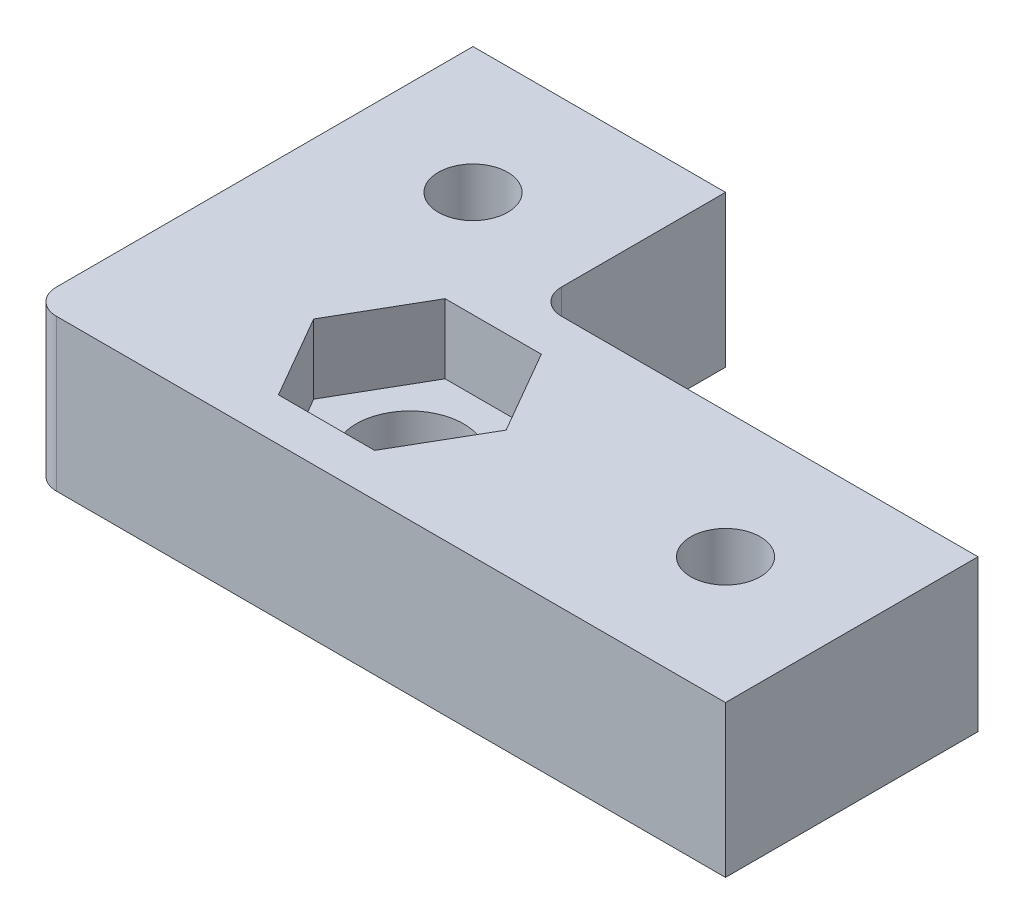
SolidWorks part; units mm, degrees
ref_plane "Alzado" through (0, 0, 0) normal (0, 0, 1) x (1, 0, 0)
ref_plane "Planta" through (0, 0, 0) normal (0, 1, 0) x (1, 0, 0)
ref_plane "Vista lateral" through (0, 0, 0) normal (1, 0, 0) x (0, 0, -1)
sketch "Croquis1" plane through (0, 0, 0) normal (0, 1, 0) x (1, 0, 0)
  line L0 (25, 65) -> (25, 25)
  line L1 (0, 0) -> (65, 0)
  line L2 (0, 0) -> (0, 65)
  line L3 (0, 65) -> (25, 65)
  line L4 (65, 0) -> (65, 25)
  line L5 (25, 25) -> (65, 25)
  line L6 (-55, 0) -> (55, 0) construction
  line L7 (0, -55) -> (0, 55) construction
  dimension "D1" = 25
  dimension "D2" = 25
  dimension "D3" = 65
  dimension "D4" = 65
extrude "Saliente-Extruir1" add sketch "Croquis1" along normal blind 12
sketch "Croquis2" plane through (0, 12, 0) normal (0, 1, 0) x (1, 0, 0)
  line L0 (0, 65) -> (0, 0)
  line L1 (0, -6.6) -> (0, 6.6) construction
  line L2 (25, 65) -> (0, 65) construction
  line L3 (0, 0) -> (65, 0)
  line L4 (-6.6, 0) -> (6.6, 0) construction
  line L5 (65, 0) -> (65, 25) construction
  line L6 (65, 0) -> (65, 5)
  line L7 (65, 5) -> (37.4, 5)
  line L8 (5, 5) -> (5, 12.6)
  line L9 (5, 65) -> (0, 65)
  line L10 (12.6, 5) -> (5, 5)
  line L11 (32.6, 5) -> (17.4, 5)
  line L12 (12.6, 5) -> (12.6, 6)
  line L13 (12.6, 6) -> (17.4, 6)
  line L14 (17.4, 5) -> (17.4, 6)
  line L15 (5, 17.4) -> (5, 65)
  line L16 (32.6, 5) -> (32.6, 6)
  line L17 (32.6, 6) -> (37.4, 6)
  line L18 (37.4, 5) -> (37.4, 6)
  line L19 (5, 17.4) -> (6, 17.4)
  line L21 (5, 12.6) -> (6, 12.6)
  line L22 (6, 17.4) -> (6, 12.6)
  dimension "D1" = 5
  dimension "D2" = 5
  dimension "D3" = 1
  dimension "D4" = 7.6
  dimension "D5" = 4.8
  dimension "D6" = 15.2
extrude "Saliente-Extruir2" add sketch "Croquis2" along normal blind 38
sketch "Croquis8" plane through (0, 50, 0) normal (0, 1, 0) x (1, 0, 0)
  line L0 (5, 17.4) -> (5, 65) construction
  line L1 (5, 25) -> (45, 25)
  line L2 (5, 25) -> (5, 5)
  line L3 (5, 5) -> (45, 5)
  line L4 (45, 25) -> (45, 5)
  line L5 (65, 5) -> (37.4, 5) construction
  dimension "D1" = 20
  dimension "D2" = 40
extrude "Cortar-Extruir5" cut sketch "Croquis8" against normal blind 20
sketch "Croquis3" plane through (0, 12, 0) normal (0, 1, 0) x (1, 0, 0)
  line L1 (5, 5) -> (5, 65) construction
  line L2 (65, 5) -> (5, 5) construction
  circle A0 centre (25, 15) radius 4.25
  dimension "D3" = 8.5
  dimension "D1" = 20
  dimension "D2" = 10
extrude "Cortar-Extruir1" cut sketch "Croquis3" against normal through all
sketch "Croquis4" plane through (0, 12, 0) normal (0, 1, 0) x (1, 0, 0)
  line L1 (32.621, 15) -> (28.8105, 21.6)
  line L2 (28.8105, 21.6) -> (21.1895, 21.6)
  line L3 (21.1895, 21.6) -> (17.379, 15)
  line L4 (17.379, 15) -> (21.1895, 8.4)
  line L5 (21.1895, 8.4) -> (28.8105, 8.4)
  line L6 (28.8105, 8.4) -> (32.621, 15)
  circle A0 centre (25, 15) radius 6.6 construction
  dimension "D1" = 13.2
extrude "Cortar-Extruir2" cut sketch "Croquis4" against normal blind 5.5
fillet "Redondeo1" radius 2 1 edges at (25, 6, -25)
sketch "Croquis5" plane through (0, 12, 0) normal (0, 1, 0) x (1, 0, 0)
  line L0 (25, 65) -> (5, 65) construction
  line L1 (12.6, 65) -> (17.4, 65)
  line L2 (12.6, 65) -> (12.6, 30)
  line L3 (12.6, 30) -> (17.4, 30)
  line L4 (17.4, 65) -> (17.4, 30)
  line L5 (5, 5) -> (5, 65) construction
  line L6 (65, 5) -> (65, 25) construction
  line L7 (65, 17.4) -> (50, 17.4)
  line L8 (65, 17.4) -> (65, 12.6)
  line L9 (65, 12.6) -> (50, 12.6)
  line L10 (50, 17.4) -> (50, 12.6)
  line L11 (65, 5) -> (37.4, 5) construction
  dimension "D1" = 35
  dimension "D2" = 4.8
  dimension "D3" = 7.6
  dimension "D4" = 15
  dimension "D5" = 7.6
extrude "Saliente-Extruir3" add sketch "Croquis5" along normal blind 1
draft "Ángulo de salida1" type of draft neutral plane draft angle 15 faces to draft 6 face at (57.5, 12.5, -17.4) face at (50, 12.5, -15) face at (57.5, 12.5, -12.6) face at (12.6, 12.5, -47.5) face at (15, 12.5, -30) face at (17.4, 12.5, -47.5) neutral plane through (0, 12, 0) neutral plane normal (0, 1, 0) parameters "D1"=15
draft "Ángulo de salida2" type of draft neutral plane draft angle 15 faces to draft 6 face at (15, 30, -5.5) face at (35, 30, -5.5) face at (37.4, 21, -5.5) face at (32.6, 21, -5.5) face at (17.4, 21, -5.5) face at (12.6, 21, -5.5) neutral plane through (65, 50, -5) neutral plane normal (0, 0, -1) parameters "D1"=15
fillet "Redondeo2" radius 2 1 edges at (0, 25, 0)
draft "Ángulo de salida3" type of draft neutral plane draft angle 15 faces to draft 3 face at (5.5, 30, -15) face at (5.5, 21, -17.4) face at (5.5, 21, -12.6) neutral plane through (5, 50, -5) neutral plane normal (1, 0, 0) parameters "D1"=15
fillet "Redondeo3" radius 1 1 edges at (5, 31, -5)
sketch "Croquis6" plane through (0, 0, 0) normal (-1, 0, 0) x (0, 0, 1)
  line L2 (-16, 45.5) -> (-14, 45.5)
  line L3 (-15, 42) -> (-15, 44.9377) construction
  line L4 (-16, 45.5) -> (-17.3031, 43.5027)
  line L5 (-14, 45.5) -> (-12.6969, 43.5027)
  line L6 (-56, 45.5) -> (-54, 45.5)
  line L7 (-55, 42) -> (-55, 46.8075) construction
  line L8 (-56, 45.5) -> (-57.3031, 43.5027)
  line L9 (-54, 45.5) -> (-52.6969, 43.5027)
  line L10 (-56, 25.5) -> (-54, 25.5)
  line L11 (-55, 22) -> (-55, 26.8846) construction
  line L12 (-56, 25.5) -> (-57.3031, 23.5027)
  line L13 (-54, 25.5) -> (-52.6969, 23.5027)
  line L14 (-5, 12) -> (-5, 50) construction
  line L15 (-17.4, 12) -> (-65, 12) construction
  arc A0 (-17.3031, 43.5027) -> (-12.6969, 43.5027) centre (-15, 42) ccw
  arc A2 (-57.3031, 43.5027) -> (-52.6969, 43.5027) centre (-55, 42) ccw
  arc A3 (-57.3031, 23.5027) -> (-52.6969, 23.5027) centre (-55, 22) ccw
  dimension "D1" = 3.5
  dimension "D11" = 2.75
  dimension "D2" = 10
  dimension "D3" = 2
  dimension "D4" = 40
  dimension "D5" = 3.5
  dimension "D6" = 2
  dimension "D7" = 3.5
  dimension "D8" = 2
  dimension "D9" = 20
  dimension "D10" = 10
extrude "Cortar-Extruir4" cut sketch "Croquis6" against normal through all
sketch "Croquis9" plane through (0, 0, 0) normal (0, 0, 1) x (1, 0, 0)
  line L0 (5, 50) -> (5, 12) construction
  line L1 (12.6, 12) -> (6, 12) construction
  line L3 (14, 45.5) -> (16, 45.5)
  line L4 (15, 42) -> (15, 46.8075) construction
  line L5 (14, 45.5) -> (12.6969, 43.5027)
  line L6 (16, 45.5) -> (17.3031, 43.5027)
  line L7 (54, 45.5) -> (56, 45.5)
  line L8 (55, 42) -> (55, 45.6308) construction
  line L9 (54, 45.5) -> (52.6969, 43.5027)
  line L10 (56, 45.5) -> (57.3031, 43.5027)
  line L11 (54, 25.5) -> (56, 25.5)
  line L12 (55, 22) -> (55, 25.3468) construction
  line L13 (54, 25.5) -> (52.6969, 23.5027)
  line L14 (56, 25.5) -> (57.3031, 23.5027)
  arc A0 (12.6969, 43.5027) -> (17.3031, 43.5027) centre (15, 42) ccw
  arc A1 (52.6969, 23.5027) -> (57.3031, 23.5027) centre (55, 22) ccw
  arc A3 (52.6969, 43.5027) -> (57.3031, 43.5027) centre (55, 42) ccw
  point P6 (9.3, 12)
  dimension "D5" = 20
  dimension "D7" = 2
  dimension "D9" = 2.75
  dimension "D10" = 50
  dimension "D1" = 10
  dimension "D2" = 3.5
  dimension "D3" = 30
  dimension "D4" = 2
  dimension "D6" = 3.5
  dimension "D8" = 3.5
extrude "Cortar-Extruir6" cut sketch "Croquis9" against normal through all
sketch "Croquis10" plane through (0, 0, 0) normal (-1, 0, 0) x (0, 0, 1)
  line L0 (-65, 50) -> (-2, 50) construction
  line L1 (-65, 50) -> (-65, 0) construction
  line L2 (-17.4, 12) -> (-65, 12) construction
  line L3 (-5, 12) -> (-5, 50) construction
  line L4 (-65, 32) -> (-5, 32) construction
  arc A0 (-25, 50) -> (-65, 32) centre (-65, 85.4444) cw
  dimension "D1" = 20
  dimension "D2" = 20
extrude "Cortar-Extruir7" [suppressed] cut sketch "Croquis10" against normal through all and the other way through all flip side to cut
sketch "Croquis11" [suppressed] plane through (0, 0, 0) normal (0, 0, 1) x (1, 0, 0)
  line L0 (65, 28) -> (5, 28) construction
  line L1 (65, 46) -> (65, 0) construction
  line L4 (25, 8) -> (25, 46) construction
  line L5 (2, 46) -> (65, 46) construction
  arc A0 (25, 46) -> (65, 28) centre (65, 81.4444) ccw
extrude "Cortar-Extruir8" [suppressed] cut sketch "Croquis11" against normal through all and the other way through all
fillet "Redondeo4" [suppressed] radius 10
sketch "Croquis12" plane through (65, 0, 0) normal (1, 0, 0) x (0, 0, -1)
  line L0 (0, 27.5) -> (0, -27.5) construction
  line L1 (0, 50) -> (65, 50)
  line L2 (0, 50) -> (0, 12)
  line L3 (0, 12) -> (65, 12)
  line L4 (65, 50) -> (65, 12)
  line L5 (0, 50) -> (5, 50) construction
extrude "Cortar-Extruir9" cut sketch "Croquis12" against normal through all
sketch "Croquis13" plane through (0, 12, 0) normal (0, 1, 0) x (1, 0, 0)
  line L0 (60, 40) -> (5, 40)
  line L2 (5, 40) -> (5, 5)
  line L4 (5, 5) -> (60, 5)
  line L5 (60, 5) -> (60, 40)
  line L7 (65, 25) -> (27, 25) construction
  line L8 (25, 27) -> (25, 65) construction
  dimension "D1" = 20
  dimension "D2" = 20
  dimension "D3" = 35
  dimension "D4" = 35
extrude "Cortar-Extruir10" cut sketch "Croquis13" against normal through all flip side to cut
fillet "Redondeo5" radius 2 1 edges at (5, 6, -5)
sketch "Croquis14" plane through (0, 12, 0) normal (0, 1, 0) x (1, 0, 0)
  line L0 (60, 15) -> (5, 15) construction
  line L1 (60, 5) -> (60, 25) construction
  line L2 (5, 40) -> (5, 7) construction
  line L3 (15, 40) -> (15, 5) construction
  line L4 (25, 40) -> (5, 40) construction
  line L5 (7, 5) -> (60, 5) construction
  circle A0 centre (15, 30) radius 2.75
  circle A1 centre (50, 15) radius 2.75
  dimension "D3" = 5.5
  dimension "D1" = 10
  dimension "D2" = 10
extrude "Cortar-Extruir11" cut sketch "Croquis14" against normal through all
